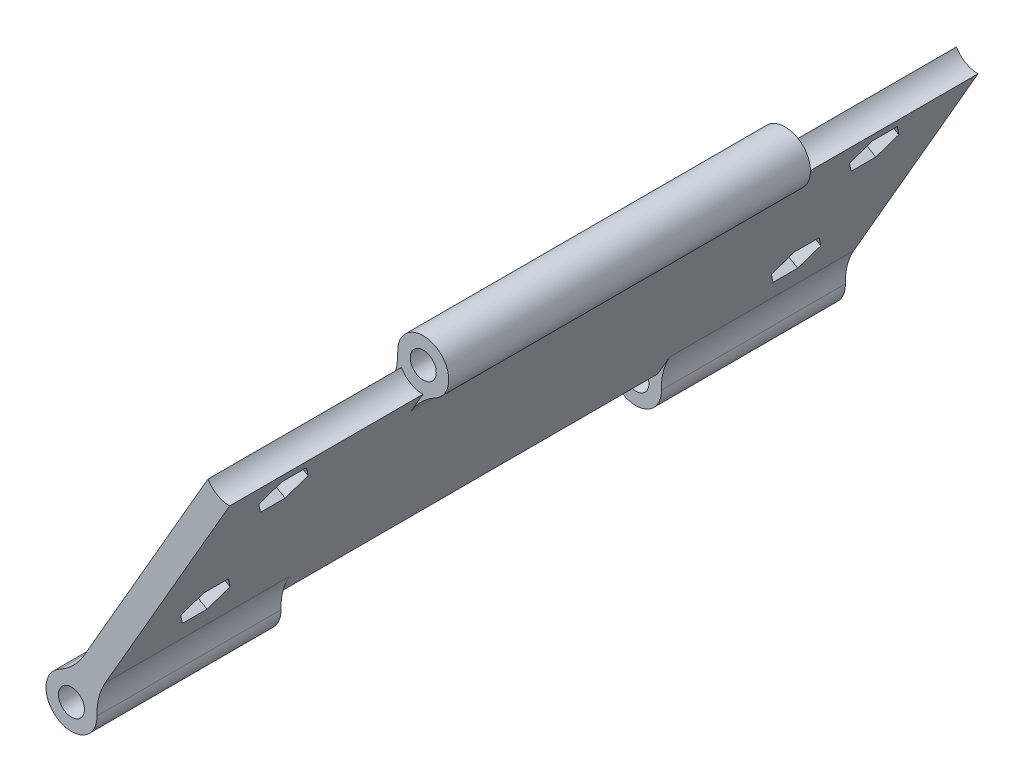
SolidWorks part; units mm, degrees
material "PLA"
ref_plane "Front Plane" through (0, 0, 0) normal (0, 0, 1) x (1, 0, 0)
ref_plane "Top Plane" through (0, 0, 0) normal (0, 1, 0) x (1, 0, 0)
ref_plane "Right Plane" through (0, 0, 0) normal (1, 0, 0) x (0, 0, -1)
sketch "Sketch2" plane through (0, 0, 0) normal (0, 0, 1) x (1, 0, 0)
  line L0 (0, 0) -> (38.1, 0)
  line L1 (0, 0) -> (0, -38.1)
  circle A0 centre (0, 0) radius 38.1
  circle A1 centre (0, -29.337) radius 1.5875
  circle A2 centre (-25.4066, 14.6685) radius 1.5875
  circle A3 centre (25.4066, 14.6685) radius 1.5875
  point P13 (0, 0)
  dimension "D1" = 76.2
  dimension "D2" = 3.175
  dimension "D3" = 8.763
  dimension "D4" = 3
extrude "Boss-Extrude1" add sketch "Sketch2" along normal blind 10 contours A1 L1 L0 A0 A3 A2 | A1 L1 A0 L0
sketch "Sketch3" plane through (0, 0, 10) normal (0, 0, 1) x (1, 0, 0)
  line L1 (0, -29.337) -> (25.4066, 14.6685)
  line L2 (1.7321, -30.337) -> (27.1386, 13.6685)
  line L3 (-1.7321, -28.337) -> (23.6745, 15.6685)
  circle A11 centre (0, -29.337) radius 1.5875
  circle A12 centre (25.4066, 14.6685) radius 1.5875
  circle A17 centre (0, -29.337) radius 2.0875
  circle A18 centre (25.4066, 14.6685) radius 2.0875
  circle A19 centre (0, -29.337) radius 4.0875
  circle A20 centre (25.4066, 14.6685) radius 4.0875
  dimension "D1" = 0.5
  dimension "D2" = 2
  dimension "D4" = 2
  dimension "D5" = 2
extrude "Boss-Extrude2" add sketch "Sketch3" along normal blind 120 separate body contours L2 A20 L3 A18 | L1 A20 L2 A18 | L3 A20 L1 A18 | A20 L1 A19 L2 | A20 L3 A19 L1 | L1 A19 L3 A17 | L2 A19 L1 A17 | L3 A19 L2 A17
delete or keep bodies "Body-Delete/Keep 2" type delete bodies bodies 101
ref_plane "Plane1" through (0, 0, 70) normal (0, 0, 1) x (1, 0, 0)
sketch "Sketch4" plane through (0, 0, 70) normal (0, 0, 1) x (1, 0, 0)
  circle A1 centre (0, -29.337) radius 4.0875
extrude "Cut-Extrude1" cut sketch "Sketch4" against normal blind 30.5 and the other way blind 30.5
sketch "Sketch5" plane through (0, 0, 10) normal (0, 0, -1) x (-1, 0, 0)
  circle A0 centre (-25.4066, 14.6685) radius 4.0875
extrude "Cut-Extrude2" cut sketch "Sketch5" against normal offset from surface (31 mm away) 1.5 up to face at (2.0875, -29.337, 39.5) offset beyond the face yes
sketch "Sketch6" plane through (0, 0, 130) normal (0, 0, 1) x (1, 0, 0)
  circle A0 centre (25.4066, 14.6685) radius 4.0875
extrude "Cut-Extrude3" cut sketch "Sketch6" against normal offset from surface (31 mm away) 1.5 contours A0 up to face at (2.0875, -29.337, 100.5) offset beyond the face yes
fillet "Fillet1" radius 10 6 edges at (21.8921, 12.5813, 70) (0.0503, -25.2498, 24.75) (0.0503, -25.2498, 115.25) (3.5144, -27.2498, 115.25) (3.5144, -27.2498, 24.75) (25.3562, 10.5813, 70)
sketch "Sketch7" plane through (10.9712, -6.3342, 0) normal (-0.866, 0.5, 0) x (0, 0, 1)
  circle A0 centre (23.772, -8.9489) radius 1.75
  circle A1 centre (23.772, 16.0955) radius 1.75
  circle A2 centre (118.4886, 16.0955) radius 1.75
  circle A3 centre (118.4886, -8.9489) radius 1.75
  dimension "D1" = 3.5
extrude "Cut-Extrude4" cut sketch "Sketch7" against normal up to surface (4 mm away) up to face at (14.7532, -7.7836, 70)
sketch "Sketch8" plane through (14.4353, -8.3343, 0) normal (0.866, -0.5, 0) x (0, 0, -1)
  line L1 (-19.8125, 16.0955) -> (-21.7922, 19.5245)
  line L2 (-21.7922, 19.5245) -> (-25.7517, 19.5245)
  line L3 (-25.7517, 19.5245) -> (-27.7314, 16.0955)
  line L4 (-27.7314, 16.0955) -> (-25.7517, 12.6665)
  line L5 (-25.7517, 12.6665) -> (-21.7922, 12.6665)
  line L6 (-21.7922, 12.6665) -> (-19.8125, 16.0955)
  line L7 (-19.8125, -8.9489) -> (-21.7922, -5.5199)
  line L8 (-21.7922, -5.5199) -> (-25.7517, -5.5199)
  line L9 (-25.7517, -5.5199) -> (-27.7314, -8.9489)
  line L10 (-27.7314, -8.9489) -> (-25.7517, -12.3779)
  line L11 (-25.7517, -12.3779) -> (-21.7922, -12.3779)
  line L12 (-21.7922, -12.3779) -> (-19.8125, -8.9489)
  line L13 (-114.5291, 16.0955) -> (-116.5088, 19.5245)
  line L14 (-116.5088, 19.5245) -> (-120.4683, 19.5245)
  line L15 (-120.4683, 19.5245) -> (-122.448, 16.0955)
  line L16 (-122.448, 16.0955) -> (-120.4683, 12.6665)
  line L17 (-120.4683, 12.6665) -> (-116.5088, 12.6665)
  line L18 (-116.5088, 12.6665) -> (-114.5291, 16.0955)
  line L25 (-114.5291, -8.9489) -> (-116.5088, -5.5199)
  line L26 (-116.5088, -5.5199) -> (-120.4683, -5.5199)
  line L27 (-120.4683, -5.5199) -> (-122.448, -8.9489)
  line L28 (-122.448, -8.9489) -> (-120.4683, -12.3779)
  line L29 (-120.4683, -12.3779) -> (-116.5088, -12.3779)
  line L30 (-116.5088, -12.3779) -> (-114.5291, -8.9489)
  circle A0 centre (-23.772, 16.0955) radius 3.429 construction
  circle A1 centre (-23.772, -8.9489) radius 3.429 construction
  circle A2 centre (-118.4886, 16.0955) radius 3.429 construction
  circle A3 centre (-118.4886, -8.9489) radius 3.429 construction
  dimension "D1" = 6.858
extrude "Cut-Extrude5" cut sketch "Sketch8" against normal blind 2.25
